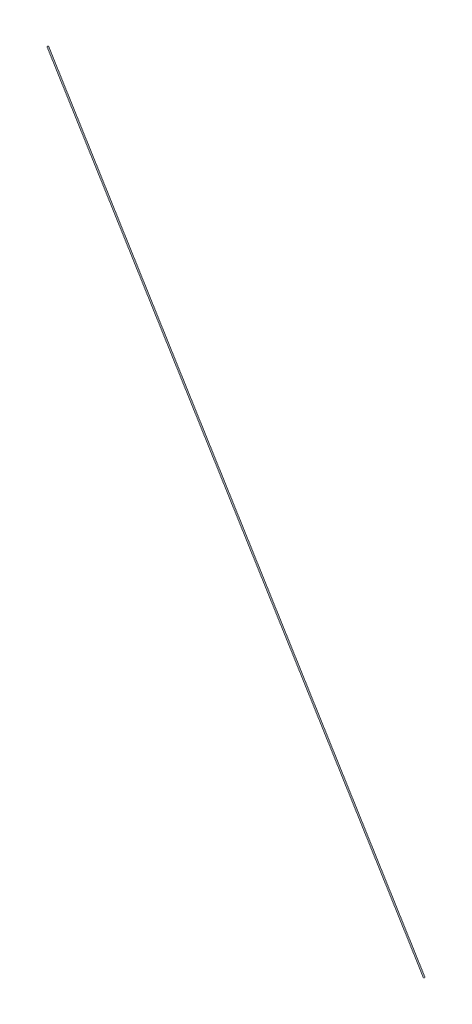
SolidWorks part; units mm, degrees
ref_plane "前视基准面" through (0, 0, 0) normal (0, 0, 1) x (1, 0, 0)
ref_plane "上视基准面" through (0, 0, 0) normal (0, 1, 0) x (1, 0, 0)
ref_plane "右视基准面" through (0, 0, 0) normal (1, 0, 0) x (0, 0, -1)
sketch "草图2" plane through (0, 0, 0) normal (0, 0, 1) x (1, 0, 0)
  line L2 (307.5, 0) -> (0, 505)
sweep "扫描1" add path "草图2" circular profile diameter 1 parameters "D3"=1
